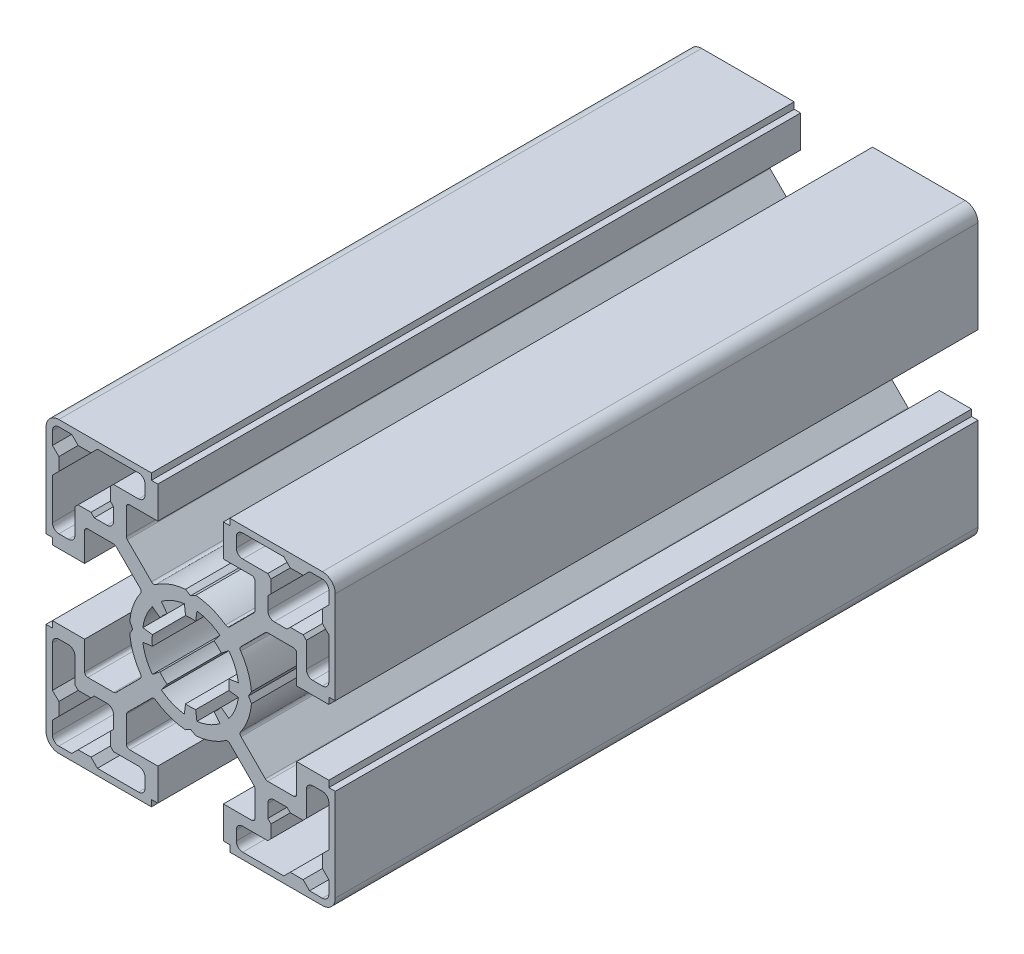
SolidWorks part; units mm, degrees
ref_plane "Ebene vorne" through (0, 0, 0) normal (0, 0, 1) x (1, 0, 0)
ref_plane "Ebene oben" through (0, 0, 0) normal (0, 1, 0) x (1, 0, 0)
ref_plane "Ebene rechts" through (0, 0, 0) normal (1, 0, 0) x (0, 0, -1)
sketch "Skizze1" plane through (0, 0, 0) normal (0, 0, 1) x (1, 0, 0)
  line L0 (14.3646, -3.3392) -> (12.8775, -3.1434)
  line L1 (11.6889, -6.0128) -> (12.879, -6.926)
  line L2 (11.4945, -8.3104) -> (10.5814, -7.1204)
  line L3 (7.712, -8.3089) -> (7.9077, -9.7961)
  line L4 (5.9499, -9.7961) -> (6.1456, -8.3089)
  line L5 (3.2762, -7.1204) -> (2.3631, -8.3104)
  line L6 (0.9787, -6.926) -> (2.1687, -6.0128)
  line L7 (0.9801, -3.1434) -> (-0.507, -3.3392)
  line L8 (-0.507, -1.3813) -> (0.9801, -1.5771)
  line L9 (2.1687, 1.2923) -> (0.9787, 2.2055)
  line L10 (2.3631, 3.5899) -> (3.2762, 2.3999)
  line L11 (6.1456, 3.5884) -> (5.9499, 5.0756)
  line L12 (7.9077, 5.0756) -> (7.712, 3.5884)
  line L13 (10.5814, 2.3999) -> (11.4945, 3.5899)
  line L14 (12.879, 2.2055) -> (11.6889, 1.2923)
  line L15 (12.8775, -1.5771) -> (14.3646, -1.3813)
  line L16 (-5.0712, 15.6398) -> (-1.1712, 15.6398)
  line L17 (-5.5712, 15.1398) -> (-5.0712, 15.6398)
  line L18 (-5.5712, 13.1398) -> (-5.5712, 15.1398)
  line L19 (-5.0712, 12.6398) -> (-5.5712, 13.1398)
  line L20 (-5.0712, 10.6398) -> (-5.0712, 12.6398)
  line L21 (-8.0712, 9.6398) -> (-6.0712, 9.6398)
  line L22 (-8.5712, 10.1398) -> (-8.0712, 9.6398)
  line L23 (-10.5712, 10.1398) -> (-8.5712, 10.1398)
  line L24 (-11.0712, 9.6398) -> (-10.5712, 10.1398)
  line L25 (-11.0712, 5.7398) -> (-11.0712, 9.6398)
  line L26 (-13.5712, 4.7398) -> (-12.0712, 4.7398)
  line L27 (-14.5712, 12.1398) -> (-14.5712, 5.7398)
  line L28 (-13.5712, 13.1398) -> (-14.5712, 12.1398)
  line L29 (-13.5712, 15.1398) -> (-13.5712, 13.1398)
  line L30 (-14.5712, 16.1398) -> (-13.5712, 15.1398)
  line L31 (-14.5712, 18.1398) -> (-14.5712, 16.1398)
  line L32 (-11.5712, 19.1398) -> (-13.5712, 19.1398)
  line L33 (-10.5712, 18.1398) -> (-11.5712, 19.1398)
  line L34 (-8.5712, 18.1398) -> (-10.5712, 18.1398)
  line L35 (-7.5712, 19.1398) -> (-8.5712, 18.1398)
  line L36 (-1.1712, 19.1398) -> (-7.5712, 19.1398)
  line L37 (-0.1712, 16.6398) -> (-0.1712, 18.1398)
  line L38 (25.9288, 4.7398) -> (27.4288, 4.7398)
  line L39 (24.9288, 9.6398) -> (24.9288, 5.7398)
  line L40 (24.4288, 10.1398) -> (24.9288, 9.6398)
  line L41 (22.4288, 10.1398) -> (24.4288, 10.1398)
  line L42 (21.9288, 9.6398) -> (22.4288, 10.1398)
  line L43 (19.9288, 9.6398) -> (21.9288, 9.6398)
  line L44 (18.9288, 12.6398) -> (18.9288, 10.6398)
  line L45 (19.4288, 13.1398) -> (18.9288, 12.6398)
  line L46 (19.4288, 15.1398) -> (19.4288, 13.1398)
  line L47 (18.9288, 15.6398) -> (19.4288, 15.1398)
  line L48 (15.0288, 15.6398) -> (18.9288, 15.6398)
  line L49 (14.0288, 18.1398) -> (14.0288, 16.6398)
  line L50 (21.4288, 19.1398) -> (15.0288, 19.1398)
  line L51 (22.4288, 18.1398) -> (21.4288, 19.1398)
  line L52 (24.4288, 18.1398) -> (22.4288, 18.1398)
  line L53 (25.4288, 19.1398) -> (24.4288, 18.1398)
  line L54 (27.4288, 19.1398) -> (25.4288, 19.1398)
  line L55 (28.4288, 16.1398) -> (28.4288, 18.1398)
  line L56 (27.4288, 15.1398) -> (28.4288, 16.1398)
  line L57 (27.4288, 13.1398) -> (27.4288, 15.1398)
  line L58 (28.4288, 12.1398) -> (27.4288, 13.1398)
  line L59 (28.4288, 5.7398) -> (28.4288, 12.1398)
  line L60 (-12.0712, -9.4602) -> (-13.5712, -9.4602)
  line L61 (-11.0712, -14.3602) -> (-11.0712, -10.4602)
  line L62 (-10.5712, -14.8602) -> (-11.0712, -14.3602)
  line L63 (-8.5712, -14.8602) -> (-10.5712, -14.8602)
  line L64 (-8.0712, -14.3602) -> (-8.5712, -14.8602)
  line L65 (-6.0712, -14.3602) -> (-8.0712, -14.3602)
  line L66 (-5.0712, -17.3602) -> (-5.0712, -15.3602)
  line L67 (-5.5712, -17.8602) -> (-5.0712, -17.3602)
  line L68 (-5.5712, -19.8602) -> (-5.5712, -17.8602)
  line L69 (-5.0712, -20.3602) -> (-5.5712, -19.8602)
  line L70 (-1.1712, -20.3602) -> (-5.0712, -20.3602)
  line L71 (-0.1712, -22.8602) -> (-0.1712, -21.3602)
  line L72 (-7.5712, -23.8602) -> (-1.1712, -23.8602)
  line L73 (-8.5712, -22.8602) -> (-7.5712, -23.8602)
  line L74 (-10.5712, -22.8602) -> (-8.5712, -22.8602)
  line L75 (-11.5712, -23.8602) -> (-10.5712, -22.8602)
  line L76 (-13.5712, -23.8602) -> (-11.5712, -23.8602)
  line L77 (-14.5712, -20.8602) -> (-14.5712, -22.8602)
  line L78 (-13.5712, -19.8602) -> (-14.5712, -20.8602)
  line L79 (-13.5712, -17.8602) -> (-13.5712, -19.8602)
  line L80 (-14.5712, -16.8602) -> (-13.5712, -17.8602)
  line L81 (-14.5712, -10.4602) -> (-14.5712, -16.8602)
  line L82 (28.4288, -16.8602) -> (28.4288, -10.4602)
  line L83 (27.4288, -17.8602) -> (28.4288, -16.8602)
  line L84 (27.4288, -19.8602) -> (27.4288, -17.8602)
  line L85 (28.4288, -20.8602) -> (27.4288, -19.8602)
  line L86 (28.4288, -22.8602) -> (28.4288, -20.8602)
  line L87 (25.4288, -23.8602) -> (27.4288, -23.8602)
  line L88 (24.4288, -22.8602) -> (25.4288, -23.8602)
  line L89 (22.4288, -22.8602) -> (24.4288, -22.8602)
  line L90 (21.4288, -23.8602) -> (22.4288, -22.8602)
  line L91 (15.0288, -23.8602) -> (21.4288, -23.8602)
  line L92 (14.0288, -21.3602) -> (14.0288, -22.8602)
  line L93 (18.9288, -20.3602) -> (15.0288, -20.3602)
  line L94 (19.4288, -19.8602) -> (18.9288, -20.3602)
  line L95 (19.4288, -17.8602) -> (19.4288, -19.8602)
  line L96 (18.9288, -17.3602) -> (19.4288, -17.8602)
  line L97 (18.9288, -15.3602) -> (18.9288, -17.3602)
  line L98 (21.9288, -14.3602) -> (19.9288, -14.3602)
  line L99 (22.4288, -14.8602) -> (21.9288, -14.3602)
  line L100 (24.4288, -14.8602) -> (22.4288, -14.8602)
  line L101 (24.9288, -14.3602) -> (24.4288, -14.8602)
  line L102 (24.9288, -10.4602) -> (24.9288, -14.3602)
  line L103 (27.4288, -9.4602) -> (25.9288, -9.4602)
  line L104 (15.9288, -2.3602) -> (16.3945, -3.1668)
  line L105 (16.3945, -1.5536) -> (15.9288, -2.3602)
  line L106 (18.5501, 7.4933) -> (14.7746, 3.7178)
  line L107 (22.9288, 7.6398) -> (18.9037, 7.6398)
  line L108 (23.4288, 2.7398) -> (23.4288, 7.1398)
  line L109 (28.4288, 2.7398) -> (23.4288, 2.7398)
  line L110 (28.4288, 3.7398) -> (28.4288, 2.7398)
  line L111 (29.4288, 3.7398) -> (28.4288, 3.7398)
  line L112 (29.4288, 18.1398) -> (29.4288, 3.7398)
  line L113 (13.0288, 20.1398) -> (27.4288, 20.1398)
  line L114 (13.0288, 19.1398) -> (13.0288, 20.1398)
  line L115 (12.0288, 19.1398) -> (13.0288, 19.1398)
  line L116 (12.0288, 14.1398) -> (12.0288, 19.1398)
  line L117 (16.4288, 14.1398) -> (12.0288, 14.1398)
  line L118 (16.9288, 9.6146) -> (16.9288, 13.6398)
  line L119 (13.0069, 5.4856) -> (16.7824, 9.2611)
  line L120 (6.9288, 6.6398) -> (7.7354, 7.1055)
  line L121 (6.1222, 7.1055) -> (6.9288, 6.6398)
  line L122 (-2.9248, 9.2611) -> (0.8507, 5.4856)
  line L123 (-3.0712, 13.6398) -> (-3.0712, 9.6146)
  line L124 (1.8288, 14.1398) -> (-2.5712, 14.1398)
  line L125 (1.8288, 19.1398) -> (1.8288, 14.1398)
  line L126 (0.8288, 19.1398) -> (1.8288, 19.1398)
  line L127 (0.8288, 20.1398) -> (0.8288, 19.1398)
  line L128 (-13.5712, 20.1398) -> (0.8288, 20.1398)
  line L129 (-15.5712, 3.7398) -> (-15.5712, 18.1398)
  line L130 (-14.5712, 3.7398) -> (-15.5712, 3.7398)
  line L131 (-14.5712, 2.7398) -> (-14.5712, 3.7398)
  line L132 (-9.5712, 2.7398) -> (-14.5712, 2.7398)
  line L133 (-9.5712, 7.1398) -> (-9.5712, 2.7398)
  line L134 (-5.0461, 7.6398) -> (-9.0712, 7.6398)
  line L135 (-0.917, 3.7178) -> (-4.6925, 7.4933)
  line L136 (-2.0712, -2.3602) -> (-2.5369, -1.5536)
  line L137 (-2.5369, -3.1668) -> (-2.0712, -2.3602)
  line L138 (-4.6925, -12.2138) -> (-0.917, -8.4383)
  line L139 (-9.0712, -12.3602) -> (-5.0461, -12.3602)
  line L140 (-9.5712, -7.4602) -> (-9.5712, -11.8602)
  line L141 (-14.5712, -7.4602) -> (-9.5712, -7.4602)
  line L142 (-14.5712, -8.4602) -> (-14.5712, -7.4602)
  line L143 (-15.5712, -8.4602) -> (-14.5712, -8.4602)
  line L144 (-15.5712, -22.8602) -> (-15.5712, -8.4602)
  line L145 (0.8288, -24.8602) -> (-13.5712, -24.8602)
  line L146 (0.8288, -23.8602) -> (0.8288, -24.8602)
  line L147 (1.8288, -23.8602) -> (0.8288, -23.8602)
  line L148 (1.8288, -18.8602) -> (1.8288, -23.8602)
  line L149 (-2.5712, -18.8602) -> (1.8288, -18.8602)
  line L150 (-3.0712, -14.3351) -> (-3.0712, -18.3602)
  line L151 (0.8507, -10.2061) -> (-2.9248, -13.9816)
  line L152 (6.9288, -11.3602) -> (6.1222, -11.8259)
  line L153 (7.7354, -11.8259) -> (6.9288, -11.3602)
  line L154 (16.7824, -13.9816) -> (13.0069, -10.2061)
  line L155 (16.9288, -18.3602) -> (16.9288, -14.3351)
  line L156 (12.0288, -18.8602) -> (16.4288, -18.8602)
  line L157 (12.0288, -23.8602) -> (12.0288, -18.8602)
  line L158 (13.0288, -23.8602) -> (12.0288, -23.8602)
  line L159 (13.0288, -24.8602) -> (13.0288, -23.8602)
  line L160 (27.4288, -24.8602) -> (13.0288, -24.8602)
  line L161 (29.4288, -8.4602) -> (29.4288, -22.8602)
  line L162 (28.4288, -8.4602) -> (29.4288, -8.4602)
  line L163 (28.4288, -7.4602) -> (28.4288, -8.4602)
  line L164 (23.4288, -7.4602) -> (28.4288, -7.4602)
  line L165 (23.4288, -11.8602) -> (23.4288, -7.4602)
  line L166 (18.9037, -12.3602) -> (22.9288, -12.3602)
  line L167 (14.7746, -8.4383) -> (18.5501, -12.2138)
  arc A0 (12.8775, -3.1434) -> (12.8775, -1.5771) centre (6.9288, -2.3602) ccw
  arc A1 (12.879, -6.926) -> (14.3646, -3.3392) centre (6.9288, -2.3602) ccw
  arc A2 (10.5814, -7.1204) -> (11.6889, -6.0128) centre (6.9288, -2.3602) ccw
  arc A3 (7.9077, -9.7961) -> (11.4945, -8.3104) centre (6.9288, -2.3602) ccw
  arc A4 (6.1456, -8.3089) -> (7.712, -8.3089) centre (6.9288, -2.3602) ccw
  arc A5 (2.3631, -8.3104) -> (5.9499, -9.7961) centre (6.9288, -2.3602) ccw
  arc A6 (2.1687, -6.0128) -> (3.2762, -7.1204) centre (6.9288, -2.3602) ccw
  arc A7 (-0.507, -3.3392) -> (0.9787, -6.926) centre (6.9288, -2.3602) ccw
  arc A8 (0.9801, -1.5771) -> (0.9801, -3.1434) centre (6.9288, -2.3602) ccw
  arc A9 (0.9787, 2.2055) -> (-0.507, -1.3813) centre (6.9288, -2.3602) ccw
  arc A10 (3.2762, 2.3999) -> (2.1687, 1.2923) centre (6.9288, -2.3602) ccw
  arc A11 (5.9499, 5.0756) -> (2.3631, 3.5899) centre (6.9288, -2.3602) ccw
  arc A12 (7.712, 3.5884) -> (6.1456, 3.5884) centre (6.9288, -2.3602) ccw
  arc A13 (11.4945, 3.5899) -> (7.9077, 5.0756) centre (6.9288, -2.3602) ccw
  arc A14 (11.6889, 1.2923) -> (10.5814, 2.3999) centre (6.9288, -2.3602) ccw
  arc A15 (14.3646, -1.3813) -> (12.879, 2.2055) centre (6.9288, -2.3602) ccw
  arc A16 (-6.0712, 9.6398) -> (-5.0712, 10.6398) centre (-6.0712, 10.6398) ccw
  arc A17 (-12.0712, 4.7398) -> (-11.0712, 5.7398) centre (-12.0712, 5.7398) ccw
  arc A18 (-14.5712, 5.7398) -> (-13.5712, 4.7398) centre (-13.5712, 5.7398) ccw
  arc A19 (-13.5712, 19.1398) -> (-14.5712, 18.1398) centre (-13.5712, 18.1398) ccw
  arc A20 (-0.1712, 18.1398) -> (-1.1712, 19.1398) centre (-1.1712, 18.1398) ccw
  arc A21 (-1.1712, 15.6398) -> (-0.1712, 16.6398) centre (-1.1712, 16.6398) ccw
  arc A22 (27.4288, 4.7398) -> (28.4288, 5.7398) centre (27.4288, 5.7398) ccw
  arc A23 (24.9288, 5.7398) -> (25.9288, 4.7398) centre (25.9288, 5.7398) ccw
  arc A24 (18.9288, 10.6398) -> (19.9288, 9.6398) centre (19.9288, 10.6398) ccw
  arc A25 (14.0288, 16.6398) -> (15.0288, 15.6398) centre (15.0288, 16.6398) ccw
  arc A26 (15.0288, 19.1398) -> (14.0288, 18.1398) centre (15.0288, 18.1398) ccw
  arc A27 (28.4288, 18.1398) -> (27.4288, 19.1398) centre (27.4288, 18.1398) ccw
  arc A28 (-13.5712, -9.4602) -> (-14.5712, -10.4602) centre (-13.5712, -10.4602) ccw
  arc A29 (-11.0712, -10.4602) -> (-12.0712, -9.4602) centre (-12.0712, -10.4602) ccw
  arc A30 (-5.0712, -15.3602) -> (-6.0712, -14.3602) centre (-6.0712, -15.3602) ccw
  arc A31 (-0.1712, -21.3602) -> (-1.1712, -20.3602) centre (-1.1712, -21.3602) ccw
  arc A32 (-1.1712, -23.8602) -> (-0.1712, -22.8602) centre (-1.1712, -22.8602) ccw
  arc A33 (-14.5712, -22.8602) -> (-13.5712, -23.8602) centre (-13.5712, -22.8602) ccw
  arc A34 (28.4288, -10.4602) -> (27.4288, -9.4602) centre (27.4288, -10.4602) ccw
  arc A35 (27.4288, -23.8602) -> (28.4288, -22.8602) centre (27.4288, -22.8602) ccw
  arc A36 (14.0288, -22.8602) -> (15.0288, -23.8602) centre (15.0288, -22.8602) ccw
  arc A37 (15.0288, -20.3602) -> (14.0288, -21.3602) centre (15.0288, -21.3602) ccw
  arc A38 (19.9288, -14.3602) -> (18.9288, -15.3602) centre (19.9288, -15.3602) ccw
  arc A39 (25.9288, -9.4602) -> (24.9288, -10.4602) centre (25.9288, -10.4602) ccw
  arc A40 (14.7182, -7.7985) -> (14.7746, -8.4383) centre (15.1282, -8.0848) ccw
  arc A41 (14.7182, -7.7985) -> (16.3945, -3.1668) centre (6.9288, -2.3602) ccw
  arc A42 (16.3945, -1.5536) -> (14.7182, 3.078) centre (6.9288, -2.3602) ccw
  arc A43 (14.7746, 3.7178) -> (14.7182, 3.078) centre (15.1282, 3.3643) ccw
  arc A44 (18.9037, 7.6398) -> (18.5501, 7.4933) centre (18.9037, 7.1398) ccw
  arc A45 (23.4288, 7.1398) -> (22.9288, 7.6398) centre (22.9288, 7.1398) ccw
  arc A46 (29.4288, 18.1398) -> (27.4288, 20.1398) centre (27.4288, 18.1398) ccw
  arc A47 (16.9288, 13.6398) -> (16.4288, 14.1398) centre (16.4288, 13.6398) ccw
  arc A48 (16.7824, 9.2611) -> (16.9288, 9.6146) centre (16.4288, 9.6146) ccw
  arc A49 (12.3671, 5.4292) -> (13.0069, 5.4856) centre (12.6533, 5.8391) ccw
  arc A50 (12.3671, 5.4292) -> (7.7354, 7.1055) centre (6.9288, -2.3602) ccw
  arc A51 (6.1222, 7.1055) -> (1.4905, 5.4292) centre (6.9288, -2.3602) ccw
  arc A52 (0.8507, 5.4856) -> (1.4905, 5.4292) centre (1.2043, 5.8391) ccw
  arc A53 (-3.0712, 9.6146) -> (-2.9248, 9.2611) centre (-2.5712, 9.6146) ccw
  arc A54 (-2.5712, 14.1398) -> (-3.0712, 13.6398) centre (-2.5712, 13.6398) ccw
  arc A55 (-13.5712, 20.1398) -> (-15.5712, 18.1398) centre (-13.5712, 18.1398) ccw
  arc A56 (-9.0712, 7.6398) -> (-9.5712, 7.1398) centre (-9.0712, 7.1398) ccw
  arc A57 (-4.6925, 7.4933) -> (-5.0461, 7.6398) centre (-5.0461, 7.1398) ccw
  arc A58 (-0.8606, 3.078) -> (-0.917, 3.7178) centre (-1.2706, 3.3643) ccw
  arc A59 (-0.8606, 3.078) -> (-2.5369, -1.5536) centre (6.9288, -2.3602) ccw
  arc A60 (-2.5369, -3.1668) -> (-0.8606, -7.7985) centre (6.9288, -2.3602) ccw
  arc A61 (-0.917, -8.4383) -> (-0.8606, -7.7985) centre (-1.2706, -8.0848) ccw
  arc A62 (-5.0461, -12.3602) -> (-4.6925, -12.2138) centre (-5.0461, -11.8602) ccw
  arc A63 (-9.5712, -11.8602) -> (-9.0712, -12.3602) centre (-9.0712, -11.8602) ccw
  arc A64 (-15.5712, -22.8602) -> (-13.5712, -24.8602) centre (-13.5712, -22.8602) ccw
  arc A65 (-3.0712, -18.3602) -> (-2.5712, -18.8602) centre (-2.5712, -18.3602) ccw
  arc A66 (-2.9248, -13.9816) -> (-3.0712, -14.3351) centre (-2.5712, -14.3351) ccw
  arc A67 (1.4905, -10.1497) -> (0.8507, -10.2061) centre (1.2043, -10.5596) ccw
  arc A68 (1.4905, -10.1497) -> (6.1222, -11.8259) centre (6.9288, -2.3602) ccw
  arc A69 (7.7354, -11.8259) -> (12.3671, -10.1497) centre (6.9288, -2.3602) ccw
  arc A70 (13.0069, -10.2061) -> (12.3671, -10.1497) centre (12.6533, -10.5596) ccw
  arc A71 (16.9288, -14.3351) -> (16.7824, -13.9816) centre (16.4288, -14.3351) ccw
  arc A72 (16.4288, -18.8602) -> (16.9288, -18.3602) centre (16.4288, -18.3602) ccw
  arc A73 (27.4288, -24.8602) -> (29.4288, -22.8602) centre (27.4288, -22.8602) ccw
  arc A74 (22.9288, -12.3602) -> (23.4288, -11.8602) centre (22.9288, -11.8602) ccw
  arc A75 (18.5501, -12.2138) -> (18.9037, -12.3602) centre (18.9037, -11.8602) ccw
  point P293 (6.9288, -2.3602)
extrude "Aufsatz-Linear austragen1" add sketch "Skizze1" along normal blind 100
